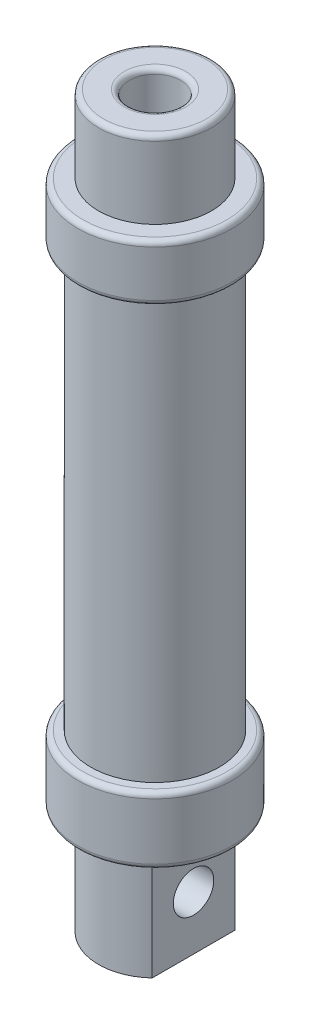
SolidWorks part; units mm, degrees
ref_plane "Front Plane" through (0, 0, 0) normal (0, 0, 1) x (1, 0, 0)
ref_plane "Top Plane" through (0, 0, 0) normal (0, 1, 0) x (1, 0, 0)
ref_plane "Right Plane" through (0, 0, 0) normal (1, 0, 0) x (0, 0, -1)
sketch "Sketch5" plane through (0, 0, 0) normal (0, 1, 0) x (1, 0, 0)
  circle A0 centre (0, 0) radius 12.5
  circle A1 centre (0, 0) radius 10.5
  dimension "D1" = 25
  dimension "D2" = 2
extrude "Boss-Extrude2" add sketch "Sketch5" along normal blind 84
sketch "Sketch6" plane through (0, 84, 0) normal (0, 1, 0) x (1, 0, 0)
  circle A0 centre (0, 0) radius 15
  circle A1 centre (0, 0) radius 11.5438
  dimension "D1" = 30
extrude "Boss-Extrude3" add sketch "Sketch6" along normal blind 10 and the other way blind 1
sketch "Sketch7" plane through (0, 0, 0) normal (0, -1, 0) x (1, 0, 0)
  circle A0 centre (0, 0) radius 15
  circle A1 centre (0, 0) radius 11.5528
  dimension "D1" = 30
extrude "Boss-Extrude4" add sketch "Sketch7" along normal blind 12 and the other way blind 1
fillet "Fillet1" radius 1 1 edges at (0, 83, 15)
fillet "Fillet2" radius 1 1 edges at (0, 1, -15)
fillet "Fillet3" radius 1 1 edges at (0, 94, 15)
fillet "Fillet4" radius 1 1 edges at (0, -12, -15)
sketch "Sketch8" plane through (0, 94, 0) normal (0, 1, 0) x (1, 0, 0)
  circle A0 centre (0, 0) radius 12.5932
extrude "Boss-Extrude5" add sketch "Sketch8" against normal blind 1
sketch "Sketch9" plane through (0, -12, 0) normal (0, -1, 0) x (1, 0, 0)
  circle A0 centre (0, 0) radius 12.7373
extrude "Boss-Extrude6" add sketch "Sketch9" against normal blind 1
sketch "Sketch10" plane through (0, -12, 0) normal (0, -1, 0) x (1, 0, 0)
  circle A0 centre (0, 0) radius 11
  dimension "D1" = 22
extrude "Boss-Extrude7" add sketch "Sketch10" along normal blind 21
sketch "Sketch11" plane through (0, -33, 0) normal (0, -1, 0) x (1, 0, 0)
  line L0 (-11, 0) -> (-7.5, 0) construction
  line L1 (-7.5, 8.0467) -> (-7.5, 0)
  line L2 (-7.5, 0) -> (-7.5, -8.0467)
  line L4 (7.5, 0) -> (7.5, -8.0467)
  line L5 (7.5, 8.0467) -> (7.5, 0)
  line L6 (7.5, 0) -> (11, 0) construction
  arc A0 (-7.5, 8.0467) -> (-7.5, -8.0467) centre (0, 0) ccw
  arc A1 (7.5, -8.0467) -> (7.5, 8.0467) centre (0, 0) ccw
  dimension "D2" = 22
  dimension "D1" = 7.5
  dimension "D3" = 8.0467
  dimension "D4" = 8.0467
extrude "Cut-Extrude1" cut sketch "Sketch11" against normal blind 21
sketch "Sketch12" plane through (-7.5, 0, 0) normal (-1, 0, 0) x (0, 0, 1)
  line L0 (8.0467, -12) -> (-8.0467, -33) construction
  line L1 (8.0467, -33) -> (-8.0467, -12) construction
  circle A0 centre (0, -22.5) radius 3.935
  dimension "D1" = 7.87
extrude "Cut-Extrude2" cut sketch "Sketch12" against normal through all
sketch "Sketch13" plane through (0, 94, 0) normal (0, 1, 0) x (1, 0, 0)
  circle A0 centre (0, 0) radius 11
  dimension "D1" = 22
extrude "Boss-Extrude8" add sketch "Sketch13" along normal blind 15
sketch "Sketch14" plane through (0, 109, 0) normal (0, 1, 0) x (1, 0, 0)
  circle A0 centre (0, 0) radius 5
  dimension "D1" = 10
extrude "Cut-Extrude3" cut sketch "Sketch14" against normal blind 20
fillet "Fillet5" radius 1 1 edges at (0, 109, 11)
fillet "Fillet6" radius 1 1 edges at (0, 109, 5)
